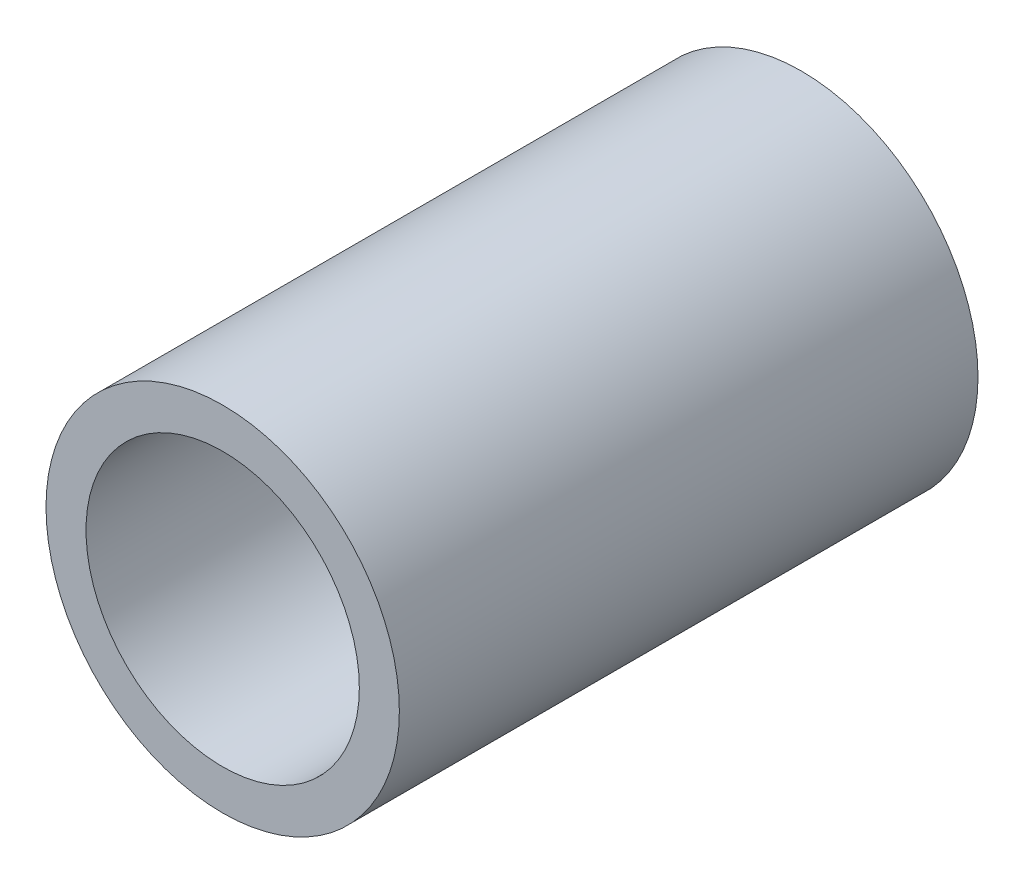
SolidWorks part; units mm, degrees
ref_plane "Plan de face" through (0, 0, 0) normal (0, 0, 1) x (1, 0, 0)
ref_plane "Plan de dessus" through (0, 0, 0) normal (0, 1, 0) x (1, 0, 0)
ref_plane "Plan de droite" through (0, 0, 0) normal (1, 0, 0) x (0, 0, -1)
sketch "Esquisse1" plane through (0, 0, 0) normal (0, 0, 1) x (1, 0, 0)
  circle A0 centre (0, 0) radius 4.415
  dimension "D1" = 8.83
extrude "Boss.-Extru.1" add sketch "Esquisse1" along normal blind 14.46
sketch "Esquisse4" plane through (0, 0, 14.46) normal (0, 0, 1) x (1, 0, 0)
  circle A0 centre (0, 0) radius 2.9
  dimension "D1" = 5.8
extrude "Enlèv. mat.-Extru.1" cut sketch "Esquisse4" against normal blind 14.46
sketch "Esquisse6" plane through (0, 0, 14.46) normal (0, 0, 1) x (1, 0, 0)
  circle A0 centre (0, 0) radius 3.415
  circle A1 centre (0, 0) radius 4.415 construction
  dimension "D1" = 1
extrude "Enlèv. mat.-Extru.2" cut sketch "Esquisse6" against normal blind 7
